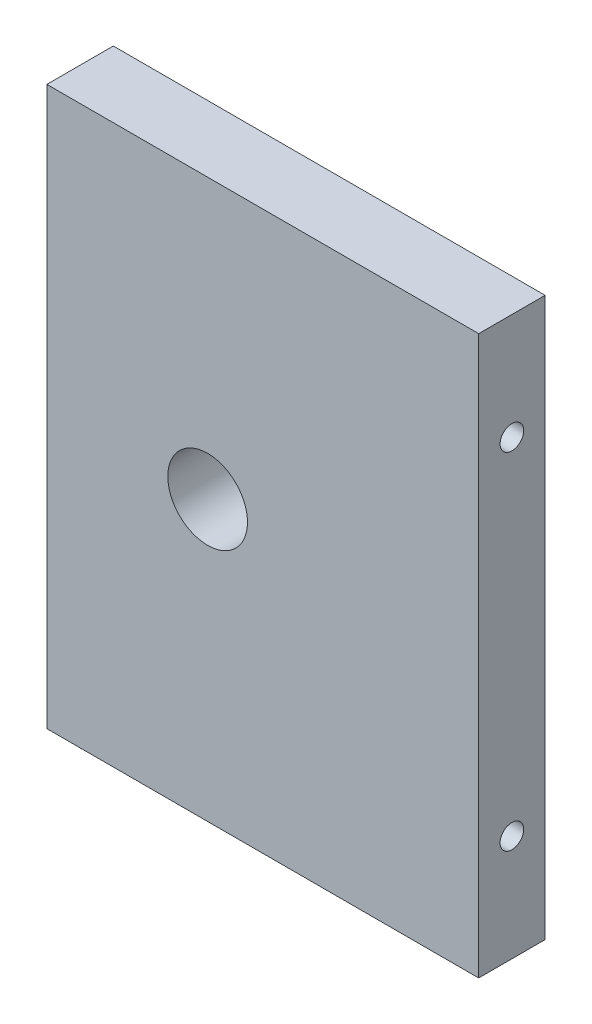
SolidWorks part; units mm, degrees
ref_plane "Front Plane" through (0, 0, 0) normal (0, 0, 1) x (1, 0, 0)
ref_plane "Top Plane" through (0, 0, 0) normal (0, 1, 0) x (1, 0, 0)
ref_plane "Right Plane" through (0, 0, 0) normal (1, 0, 0) x (0, 0, -1)
sketch "Sketch1" plane through (0, 0, 0) normal (0, 0, 1) x (1, 0, 0)
  line L1 (0, 0) -> (32.5, 0)
  line L2 (0, 0) -> (0, 42)
  line L3 (0, 42) -> (32.5, 42)
  line L4 (32.5, 0) -> (32.5, 42)
extrude "Boss-Extrude2" add sketch "Sketch1" along normal blind 5
sketch "Sketch2" plane through (0, 0, 5) normal (0, 0, 1) x (1, 0, 0)
  line L0 (0, 42) -> (0, 34)
  line L1 (0, 42) -> (0, 0) construction
  line L2 (0, 34) -> (32.5, 34)
  line L3 (32.5, 0) -> (32.5, 42) construction
  line L4 (0, 0) -> (0, 8)
  line L5 (0, 8) -> (32.5, 8)
sketch "Sketch3" plane through (0, 0, 0) normal (-1, 0, 0) x (0, 0, 1)
  line L0 (5, 34) -> (0, 34)
  line L1 (5, 42) -> (5, 34) construction
  line L2 (0, 42) -> (0, 0) construction
  line L3 (5, 8) -> (0, 8)
  line L4 (5, 0) -> (5, 8) construction
  line L5 (5, 42) -> (5, 0) construction
hole_wizard "#2-56 Tapped Hole1" positions "Sketch4" profile "Sketch5" tap size "#2-56" standard "ANSI Inch"
sketch "Sketch4" plane through (0, 0, 0) normal (-1, 0, 0) x (0, 0, 1)
  line L0 (5, 34) -> (0, 34) construction
  line L1 (5, 8) -> (0, 8) construction
  point P0 (2.5, 34)
  point P4 (2.5, 8)
sketch "Sketch5" plane through (0, 34, 2.5) normal (0, 1, 0) x (0, 0, 1)
  line L0 (0, 0) -> (0, 8)
  line L1 (0, 8) -> (0.889, 7.4658)
  line L2 (0.889, 7.4658) -> (0.889, 0)
  line L5 (0.889, 0) -> (0, 0)
  line L10 (0, 8) -> (-0.889, 7.4658) construction
  line L11 (0, -6.35) -> (0, 107.95) construction
  dimension "Tap Drill Dia." = 1.778
  dimension "Tap Drill Depth" = 8
  dimension "Drill Angle" = 118
cosmetic thread "Hole Thread1" parameters "D1"=4.37, "D2"=2.1844
cosmetic thread "Hole Thread2" parameters "D1"=4.37, "D2"=2.1844
sketch "Sketch6" plane through (32.5, 0, 0) normal (1, 0, 0) x (0, 0, -1)
  line L0 (-5, 34) -> (0, 34)
  line L1 (-5, 8) -> (0, 8)
hole_wizard "#2-56 Tapped Hole2" positions "Sketch7" profile "Sketch8" tap size "#2-56" standard "ANSI Inch"
sketch "Sketch7" plane through (32.5, 0, 0) normal (1, 0, 0) x (0, 0, -1)
  point P0 (-2.5, 34)
  point P3 (-2.5, 8)
sketch "Sketch8" plane through (32.5, 34, 2.5) normal (0, 1, 0) x (0, 0, -1)
  line L0 (0, 0) -> (0, 8)
  line L1 (0, 8) -> (0.889, 7.4658)
  line L2 (0.889, 7.4658) -> (0.889, 0)
  line L5 (0.889, 0) -> (0, 0)
  line L10 (0, 8) -> (-0.889, 7.4658) construction
  line L11 (0, -6.35) -> (0, 107.95) construction
  dimension "Tap Drill Dia." = 1.778
  dimension "Tap Drill Depth" = 8
  dimension "Drill Angle" = 118
cosmetic thread "Hole Thread3" parameters "D1"=4.37, "D2"=2.1844
cosmetic thread "Hole Thread4" parameters "D1"=4.37, "D2"=2.1844
sketch "Sketch9" plane through (0, 0, 0) normal (0, 0, -1) x (-1, 0, 0)
  line L0 (0, 21) -> (-32.5, 21)
  line L1 (0, 42) -> (0, 0) construction
  line L2 (-32.5, 0) -> (-32.5, 42) construction
  line L3 (-16.25, 21) -> (-12.1, 21)
  circle A0 centre (-12.1, 21) radius 3
  point P9 (-10.628, 21)
  point P10 (0, 0)
  point P11 (-12.1769, 21)
extrude "Cut-Extrude1" cut sketch "Sketch9" against normal blind 5 contours L0 A0 | L0 A0
sketch "Sketch10" plane through (0, 0, 0) normal (0, 0, -1) x (-1, 0, 0)
  line L0 (-32.5, 42) -> (0, 0)
